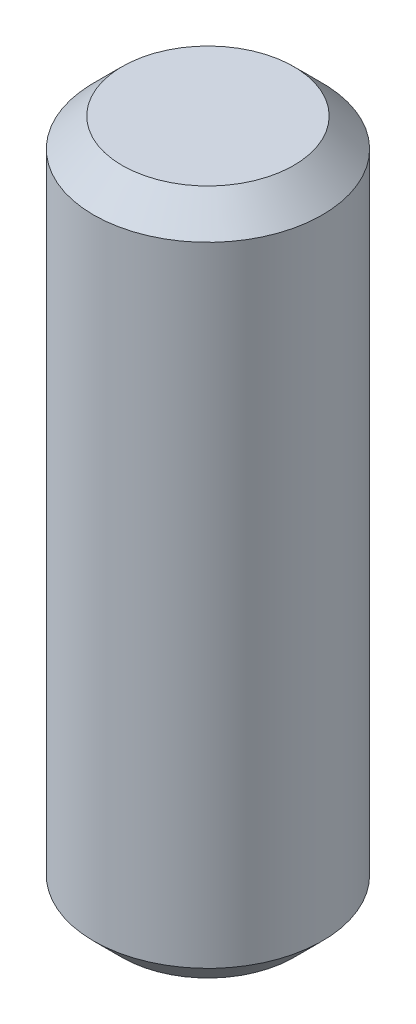
SolidWorks part; units mm, degrees
ref_plane "Front Plane" through (0, 0, 0) normal (0, 0, 1) x (1, 0, 0)
ref_plane "Top Plane" through (0, 0, 0) normal (0, 1, 0) x (1, 0, 0)
ref_plane "Right Plane" through (0, 0, 0) normal (1, 0, 0) x (0, 0, -1)
sketch "Sketch1" plane through (0, 0, 0) normal (0, 1, 0) x (1, 0, 0)
  circle A0 centre (0, 0) radius 2
  dimension "D1" = 4
extrude "Boss-Extrude1" add sketch "Sketch1" along normal blind 12
chamfer "Chamfer1" distance 0.5 angle 45 2 edges at (0, 0, 2) (0, 12, 2)
